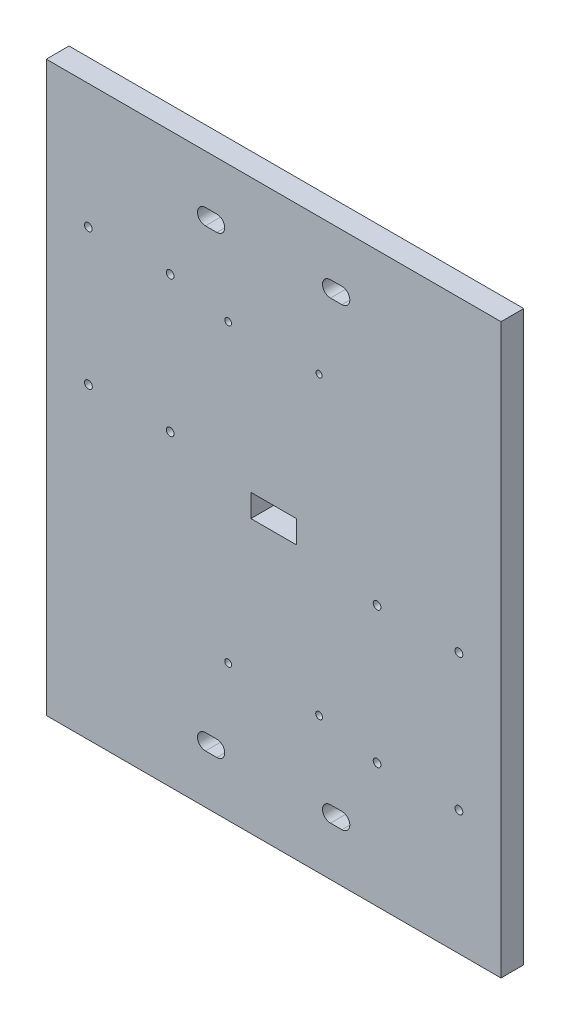
SolidWorks part; units mm, degrees
ref_plane "Plan de face" through (0, 0, 0) normal (0, 0, 1) x (1, 0, 0)
ref_plane "Plan de dessus" through (0, 0, 0) normal (0, 1, 0) x (1, 0, 0)
ref_plane "Plan de droite" through (0, 0, 0) normal (1, 0, 0) x (0, 0, -1)
sketch "Esquisse2" plane through (0, 0, 0) normal (0, 0, 1) x (1, 0, 0)
  line L1 (0, 0) -> (200, 0)
  line L2 (0, 0) -> (0, -250)
  line L3 (0, -250) -> (200, -250)
  line L4 (200, 0) -> (200, -250)
  dimension "D1" = 200
  dimension "D2" = 250
extrude "Boss.-Extru.1" add sketch "Esquisse2" along normal blind 10 contours L1 L4 L3 L2
sketch "Esquisse7" plane through (0, 0, 0) normal (0, 0, -1) x (-1, 0, 0)
  line L0 (0, 0) -> (-200, 0) construction
  line L1 (-110, -130) -> (-90, -130)
  line L2 (-110, -130) -> (-110, -120)
  line L3 (-110, -120) -> (-90, -120)
  line L4 (-90, -130) -> (-90, -120)
  line L6 (-200, 0) -> (-200, -250) construction
  line L7 (0, 0) -> (0, -250) construction
  line L8 (0, -250) -> (-200, -250) construction
  dimension "D1" = 10
  dimension "D2" = 120
  dimension "D3" = 90
  dimension "D4" = 90
extrude "Enlèv. mat.-Extru.2" cut sketch "Esquisse7" against normal blind 10
sketch "Esquisse9" plane through (0, 0, 10) normal (0, 0, 1) x (1, 0, 0)
  line L0 (0, 0) -> (0, -250) construction
  line L1 (200, 0) -> (200, -250) construction
  circle A0 centre (5, -50.3051) radius 3
  circle A1 centre (195, -50.3051) radius 3
  dimension "D1" = 6
  dimension "D2" = 6
  dimension "D3" = 5
  dimension "D4" = 5
extrude "Boss.-Extru.2" [suppressed] add sketch "Esquisse9" along normal blind 6
fillet "Congé3" [suppressed] radius 2
sketch "Esquisse10" plane through (0, 0, 0) normal (0, 0, -1) x (-1, 0, 0)
  line L0 (-70, -25) -> (-75, -25) construction
  line L1 (-70, -28.5) -> (-75, -28.5)
  line L2 (-70, -21.5) -> (-75, -21.5)
  line L3 (-70, -225) -> (-75, -225) construction
  line L4 (-70, -228.5) -> (-75, -228.5)
  line L5 (-70, -221.5) -> (-75, -221.5)
  line L6 (-130, -225) -> (-125, -225) construction
  line L7 (-130, -221.5) -> (-125, -221.5)
  line L8 (-130, -228.5) -> (-125, -228.5)
  line L9 (-130, -25) -> (-125, -25) construction
  line L10 (-130, -21.5) -> (-125, -21.5)
  line L11 (-130, -28.5) -> (-125, -28.5)
  line L12 (0, 0) -> (-200, 0) construction
  line L14 (0, -250) -> (-200, -250) construction
  line L16 (-127.5, 0) -> (-127.5, -250) construction
  line L17 (-72.5, 0) -> (-72.5, -250) construction
  line L21 (-110, -120) -> (-110, -130) construction
  line L22 (-90, -130) -> (-90, -120) construction
  line L24 (-200, 0) -> (-200, -250) construction
  arc A0 (-70, -28.5) -> (-70, -21.5) centre (-70, -25) ccw
  arc A1 (-75, -21.5) -> (-75, -28.5) centre (-75, -25) ccw
  arc A2 (-70, -228.5) -> (-70, -221.5) centre (-70, -225) ccw
  arc A3 (-75, -221.5) -> (-75, -228.5) centre (-75, -225) ccw
  arc A4 (-130, -221.5) -> (-130, -228.5) centre (-130, -225) ccw
  arc A5 (-125, -228.5) -> (-125, -221.5) centre (-125, -225) ccw
  arc A6 (-130, -21.5) -> (-130, -28.5) centre (-130, -25) ccw
  arc A7 (-125, -28.5) -> (-125, -21.5) centre (-125, -25) ccw
  point P2 (-72.5, -25)
  point P7 (-72.5, -225)
  point P14 (-127.5, -225)
  point P21 (-127.5, -25)
  point P36 (-121.5, -225)
  point P37 (-78.5, -225)
  point P38 (-133.5, -225)
  point P41 (-110, -125)
  point P44 (-90, -125)
  point P45 (-66.5, -225)
  point P46 (-121.5, -25)
  point P47 (-78.5, -25)
  dimension "D2" = 43
  dimension "D3" = 5
  dimension "D4" = 7
  dimension "D5" = 7
  dimension "D6" = 0
  dimension "D7" = 100
  dimension "D8" = 72.5
  dimension "D9" = 5
  dimension "D10" = 7
  dimension "D11" = 100
  dimension "D12" = 0
  dimension "D13" = 7
  dimension "D14" = 5
  dimension "D15" = 100
  dimension "D16" = 0
  dimension "D17" = 0
  dimension "D18" = 100
  dimension "D19" = 5
extrude "Enlèv. mat.-Extru.3" cut sketch "Esquisse10" against normal blind 10
sketch "Esquisse11" plane through (0, 0, 0) normal (0, 0, -1) x (-1, 0, 0)
  line L0 (-90, -130) -> (-90, -120) construction
  line L4 (-90, -120) -> (-110, -120) construction
  circle A0 centre (-80, -190) radius 1.5
  circle A1 centre (-120, -190) radius 1.5
  circle A2 centre (-80, -60) radius 1.5
  circle A3 centre (-120, -60) radius 1.3766
  dimension "D3" = 3
  dimension "D4" = 3
  dimension "D5" = 3
  dimension "D1" = 40
  dimension "D2" = 10
  dimension "D6" = 40
  dimension "D7" = 130
  dimension "D8" = 60
extrude "Enlèv. mat.-Extru.4" cut sketch "Esquisse11" against normal blind 10
sketch "Esquisse12" plane through (0, 0, 0) normal (0, 0, -1) x (-1, 0, 0)
  line L4 (-118.6234, -60) -> (0, -60) construction
  line L5 (0, 0) -> (0, -250) construction
  line L6 (0, -54.7) -> (-200, -54.7) construction
  line L7 (-200, 0) -> (-200, -250) construction
  line L9 (-121.5, -190) -> (0, -190) construction
  line L10 (0, -190) -> (-200, -190) construction
  line L11 (0, -191.5) -> (0, -195.3) construction
  line L12 (0, -195.3) -> (-200, -195.3) construction
  circle A10 centre (-120, -60) radius 1.3766 construction
  circle A13 centre (-120, -190) radius 1.5 construction
  point P2 (0, 0)
  point P15 (-54.5, -54.7)
  point P19 (-18.5, -54.7)
  point P21 (-54.5, -114.7)
  point P22 (-18.5459, -114.7)
  point P29 (-145.5, -195.3)
  point P34 (-181.5, -195.3)
  point P35 (-181.5, -135.3)
  point P36 (-145.5, -135.3)
  dimension "D1" = 5.3
  dimension "D2" = 18.5
  dimension "D6" = 18.5
  dimension "D3" = 36
  dimension "D4" = 60
  dimension "D5" = 5.3
  dimension "D7" = 36
  dimension "D8" = 60
  dimension "D9" = 36
sketch "Esquisse13" plane through (0, 0, 0) normal (0, 0, -1) x (-1, 0, 0)
  line L0 (-130, -28.5) -> (-125, -28.5) construction
  line L1 (-133.55, -228.55) -> (-121.45, -228.55)
  line L2 (-133.55, -228.55) -> (-133.55, -221.45)
  line L3 (-133.55, -221.45) -> (-121.45, -221.45)
  line L4 (-121.45, -228.55) -> (-121.45, -221.45)
  line L5 (-78.55, -228.55) -> (-66.45, -228.55)
  line L6 (-78.55, -228.55) -> (-78.55, -221.45)
  line L7 (-78.55, -221.45) -> (-66.45, -221.45)
  line L8 (-66.45, -228.55) -> (-66.45, -221.45)
  line L9 (-133.55, -28.55) -> (-121.45, -28.55)
  line L10 (-133.55, -28.55) -> (-133.55, -21.45)
  line L11 (-133.55, -21.45) -> (-121.45, -21.45)
  line L12 (-121.45, -28.55) -> (-121.45, -21.45)
  line L13 (-78.55, -28.55) -> (-66.45, -28.55)
  line L14 (-78.55, -28.55) -> (-78.55, -21.45)
  line L15 (-78.55, -21.45) -> (-66.45, -21.45)
  line L16 (-66.45, -28.55) -> (-66.45, -21.45)
  line L17 (-75, -28.5) -> (-70, -28.5) construction
  line L18 (-75, -228.5) -> (-70, -228.5) construction
  line L19 (-130, -228.5) -> (-125, -228.5) construction
  arc A0 (-130, -21.5) -> (-130, -28.5) centre (-130, -25) ccw construction
  arc A1 (-75, -21.5) -> (-75, -28.5) centre (-75, -25) ccw construction
  arc A2 (-75, -221.5) -> (-75, -228.5) centre (-75, -225) ccw construction
  arc A3 (-130, -221.5) -> (-130, -228.5) centre (-130, -225) ccw construction
  point P21 (-133.5, -25)
  point P25 (-78.5, -25)
  point P31 (-78.5, -225)
  point P39 (-133.5, -225)
  dimension "D1" = 12.1
  dimension "D2" = 7.1
  dimension "D3" = 0.05
  dimension "D4" = 0.05
  dimension "D5" = 7.1
  dimension "D6" = 12.1
  dimension "D7" = 0.05
  dimension "D8" = 0.05
  dimension "D9" = 12.1
  dimension "D10" = 7.1
  dimension "D11" = 0.05
  dimension "D12" = 0.05
  dimension "D13" = 12.1
  dimension "D14" = 7.1
  dimension "D15" = 0.05
  dimension "D16" = 0.05
split line "Ligne de séparation1"
hole_wizard "Dégagement M31" positions "Esquisse15" profile "Esquisse16" hole size "M3" standard "ISO" end condition through all
sketch "Esquisse15" plane through (0, 0, 10) normal (0, 0, 1) x (1, 0, 0)
  point P0 (18.5, -54.7)
  point P3 (54.5, -54.7)
  point P6 (18.5459, -114.7)
  point P9 (54.5, -114.7)
  point P12 (145.5, -135.3)
  point P15 (181.5, -135.3)
  point P18 (145.5, -195.3)
  point P21 (181.5, -195.3)
sketch "Esquisse16" plane through (18.5, -54.7, 10) normal (1, 0, 0) x (0, -1, 0)
  line L0 (0, 0) -> (0, 10)
  line L1 (0, 10) -> (1.7, 10)
  line L2 (1.7, 10) -> (1.7, 0)
  line L5 (1.7, 0) -> (0, 0)
  line L11 (0, -6.35) -> (0, 107.95) construction
  dimension "Diamètre du perçage jusqu'au prochain" = 3.4
  dimension "Profondeur du perçage jusqu'au prochain" = 10
